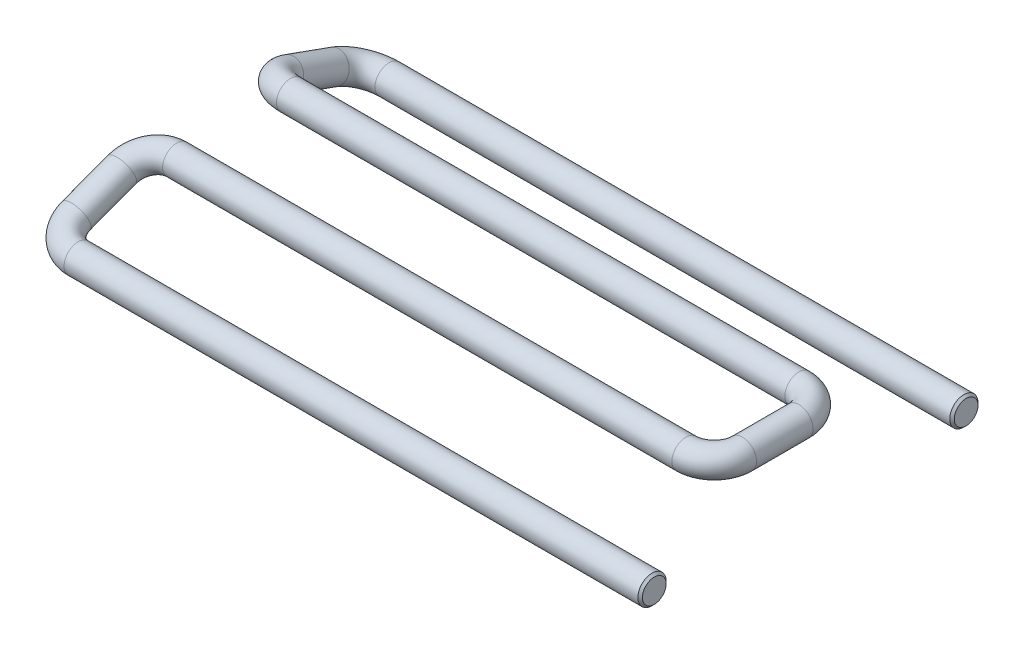
SolidWorks part; units mm, degrees
material "Plain Carbon Steel"
ref_plane "Front Plane" through (0, 0, 0) normal (0, 0, 1) x (1, 0, 0)
ref_plane "Top Plane" through (0, 0, 0) normal (0, 1, 0) x (1, 0, 0)
ref_plane "Right Plane" through (0, 0, 0) normal (1, 0, 0) x (0, 0, -1)
sketch3d "3DSketch1"
  line L0 (3.1945, 0, 0) -> (68.0913, 0, 0)
  line L1 (0.0195, 1.0924, 3.0018) -> (0.053, 2.9648, 8.1472)
  line L2 (0, 0, 0) -> (0, 0, 6.8979) construction
  line L3 (3.2279, 4.044, 11.1125) -> (60.3973, 4.044, 11.1125)
  line L4 (63.5723, 4.044, 14.2875) -> (63.5723, 4.044, 20.6375)
  line L5 (60.3973, 4.044, 23.8125) -> (3.1222, 4.044, 23.8125)
  line L6 (-0.0527, 2.9516, 26.8143) -> (-0.0193, 1.0791, 31.9597)
  line L7 (0, 0, 34.925) -> (0, 0, 18.874) construction
  line L8 (3.1557, 0, 34.925) -> (67.945, 0, 34.925)
  arc A0 (-0.0193, 1.0791, 31.9597) -> (3.1557, 0, 34.925) centre (3.1557, 1.0858, 31.9414) ccw
  arc A1 (3.1222, 4.044, 23.8125) -> (-0.0527, 2.9516, 26.8143) centre (3.1222, 2.9582, 26.7961) ccw
  arc A2 (63.5723, 4.044, 20.6375) -> (60.3973, 4.044, 23.8125) centre (60.3973, 4.044, 20.6375) ccw
  arc A3 (60.3973, 4.044, 11.1125) -> (63.5723, 4.044, 14.2875) centre (60.3973, 4.044, 14.2875) ccw
  arc A4 (0.053, 2.9648, 8.1472) -> (3.2279, 4.044, 11.1125) centre (3.2279, 2.9582, 8.1289) ccw
  arc A5 (3.1945, 0, 0) -> (0.0195, 1.0924, 3.0018) centre (3.1945, 1.0858, 2.9836) ccw
  point P13 (0, 0, 34.925)
  point P15 (3.1557, 4.0693, 33.0272)
  point P18 (-0.0723, 4.044, 23.8125)
  point P19 (3.1222, 5.9418, 27.8818)
  point P22 (63.5723, 4.044, 23.8125)
  point P23 (60.3973, 0.869, 20.6375)
  point P26 (63.5723, 4.044, 11.1125)
  point P27 (60.3973, 0.869, 14.2875)
  point P30 (0.0723, 4.044, 11.1125)
  point P31 (3.2279, 5.9418, 7.0432)
  point P34 (0, 0, 0)
  point P36 (3.1945, 4.0693, 1.8978)
  dimension "D9" = 3.175
  dimension "D1" = 20
  dimension "D2" = 20
  dimension "D3" = 68.0913
  dimension "D4" = 63.5
  dimension "D5" = 12.7
  dimension "D6" = 63.6445
  dimension "D7" = 67.945
  dimension "D8" = 34.925
ref_plane "Plane1" through (67.945, 0, 0) normal (1, 0, 0) x (0, 0, -1)
sketch "Sketch1" plane through (67.945, 0, 0) normal (1, 0, 0) x (0, 0, -1)
  circle A0 centre (-34.925, 0) radius 1.5875
sweep "Sweep1" add profiles "Sketch1" path "3DSketch1"
chamfer "Chamfer1" distance 0.254 angle 45 2 edges at (68.0913, 0, 1.5875) (67.945, 0, 33.3375)
